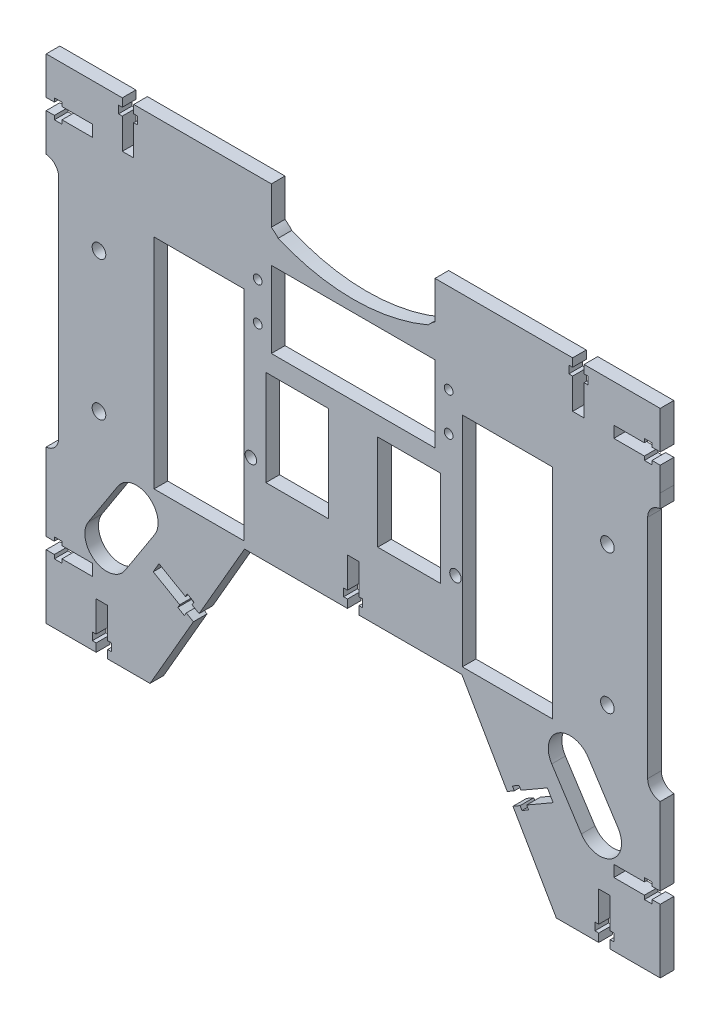
SolidWorks part; units mm, degrees
ref_plane "Front Plane" through (0, 0, 0) normal (0, 0, 1) x (1, 0, 0)
ref_plane "Top Plane" through (0, 0, 0) normal (0, 1, 0) x (1, 0, 0)
ref_plane "Right Plane" through (0, 0, 0) normal (1, 0, 0) x (0, 0, -1)
sketch "Sketch1" plane through (0, 0, 0) normal (0, 0, 1) x (1, 0, 0)
  line L40 (-72.729, 26.6154) -> (-39.729, 26.6154)
  line L41 (-72.729, 26.6154) -> (-72.729, -53.3846)
  line L42 (-72.729, -53.3846) -> (-39.729, -53.3846)
  line L43 (-39.729, 26.6154) -> (-39.729, -53.3846)
  line L44 (-72.729, 26.6154) -> (-39.729, -53.3846) construction
  line L45 (-72.729, -53.3846) -> (-39.729, 26.6154) construction
  line L46 (-35.729, 4.1154) -> (-4.729, 4.1154)
  line L47 (-35.729, 4.1154) -> (-35.729, -30.8846)
  line L48 (-35.729, -30.8846) -> (-4.729, -30.8846)
  line L49 (-4.729, 4.1154) -> (-4.729, -30.8846)
  line L50 (-35.729, 4.1154) -> (-4.729, -30.8846) construction
  line L51 (-35.729, -30.8846) -> (-4.729, 4.1154) construction
  line L52 (5.271, 4.1154) -> (36.271, 4.1154)
  line L53 (5.271, 4.1154) -> (5.271, -30.8846)
  line L54 (5.271, -30.8846) -> (36.271, -30.8846)
  line L55 (36.271, 4.1154) -> (36.271, -30.8846)
  line L56 (5.271, 4.1154) -> (36.271, -30.8846) construction
  line L57 (5.271, -30.8846) -> (36.271, 4.1154) construction
  line L58 (71.8624, -120.8846) -> (117.841, -120.8846)
  line L59 (117.841, -120.8846) -> (117.841, -59.8774)
  line L60 (117.841, -59.8774) -> (113.241, -59.8774)
  line L61 (108.241, -54.8774) -> (108.241, 28.1082)
  line L62 (113.241, 33.1082) -> (117.8396, 33.1082)
  line L63 (117.8396, 33.1082) -> (117.8393, 49.9036)
  line L64 (117.8393, 49.9036) -> (117.8223, 69.9688)
  line L65 (117.8223, 69.9688) -> (36.9219, 69.9688)
  line L66 (-36.3799, 69.9688) -> (-117.2803, 69.9688)
  line L67 (-117.2803, 69.9688) -> (-117.2973, 49.9036)
  line L68 (-117.2973, 49.9036) -> (-117.2977, 33.1082)
  line L69 (-117.2977, 33.1082) -> (-112.699, 33.1082)
  line L70 (-107.699, 28.1082) -> (-107.699, -54.8774)
  line L71 (-112.699, -59.8774) -> (-117.299, -59.8774)
  line L72 (-117.299, -59.8774) -> (-117.299, -120.8846)
  line L73 (-117.299, -120.8846) -> (-71.3205, -120.8846)
  line L74 (-71.3205, -120.8846) -> (-36.6794, -60.8846)
  line L75 (-36.6794, -60.8846) -> (37.2214, -60.8846)
  line L76 (37.2214, -60.8846) -> (71.8624, -120.8846)
  line L77 (71.8624, -120.8846) -> (117.841, -120.8846)
  line L78 (117.841, -120.8846) -> (117.841, -59.8774)
  line L79 (117.841, -59.8774) -> (113.241, -59.8774)
  line L80 (108.241, -54.8774) -> (108.241, 28.1082)
  line L81 (113.241, 33.1082) -> (117.8396, 33.1082)
  line L82 (117.8396, 33.1082) -> (117.8393, 49.9036)
  line L83 (117.8393, 49.9036) -> (117.8223, 69.9688)
  line L84 (117.8223, 69.9688) -> (36.9219, 69.9688)
  line L85 (-36.3799, 69.9688) -> (-117.2803, 69.9688)
  line L86 (-117.2803, 69.9688) -> (-117.2973, 49.9036)
  line L87 (-117.2973, 49.9036) -> (-117.2977, 33.1082)
  line L88 (-117.2977, 33.1082) -> (-112.699, 33.1082)
  line L89 (-107.699, 28.1082) -> (-107.699, -54.8774)
  line L90 (-112.699, -59.8774) -> (-117.299, -59.8774)
  line L91 (-117.299, -59.8774) -> (-117.299, -120.8846)
  line L92 (-117.299, -120.8846) -> (-71.3205, -120.8846)
  line L93 (-71.3205, -120.8846) -> (-36.6794, -60.8846)
  line L94 (-36.6794, -60.8846) -> (37.2214, -60.8846)
  line L95 (37.2214, -60.8846) -> (71.8624, -120.8846)
  line L96 (40.271, 26.6154) -> (73.271, 26.6154)
  line L97 (40.271, 26.6154) -> (40.271, -53.3846)
  line L98 (40.271, -53.3846) -> (73.271, -53.3846)
  line L99 (73.271, 26.6154) -> (73.271, -53.3846)
  line L100 (40.271, 26.6154) -> (73.271, -53.3846) construction
  line L101 (40.271, -53.3846) -> (73.271, 26.6154) construction
  circle A37 centre (-92.929, 12.1154) radius 2.5
  circle A38 centre (-92.929, -38.8846) radius 2.5
  circle A39 centre (93.471, 12.1154) radius 2.5
  circle A40 centre (93.471, -38.8846) radius 2.5
  arc A42 (108.241, -54.8774) -> (113.241, -59.8774) centre (113.241, -54.8774) ccw
  arc A43 (113.241, 33.1082) -> (108.241, 28.1082) centre (113.241, 28.1082) ccw
  arc A44 (-36.3799, 69.9688) -> (36.9219, 69.9688) centre (0.271, 135.4036) ccw
  arc A45 (-107.699, 28.1082) -> (-112.699, 33.1082) centre (-112.699, 28.1082) ccw
  arc A46 (-112.699, -59.8774) -> (-107.699, -54.8774) centre (-112.699, -54.8774) ccw
  arc A47 (108.241, -54.8774) -> (113.241, -59.8774) centre (113.241, -54.8774) ccw
  arc A48 (113.241, 33.1082) -> (108.241, 28.1082) centre (113.241, 28.1082) ccw
  arc A49 (-36.3799, 69.9688) -> (36.9219, 69.9688) centre (0.271, 135.4036) ccw
  arc A50 (-107.699, 28.1082) -> (-112.699, 33.1082) centre (-112.699, 28.1082) ccw
  arc A51 (-112.699, -59.8774) -> (-107.699, -54.8774) centre (-112.699, -54.8774) ccw
  point P18 (-56.229, -13.3846)
  point P27 (-20.229, -13.3846)
  point P36 (20.771, -13.3846)
  point P45 (56.771, -13.3846)
  dimension "D1" = 0
extrude "Boss-Extrude1" add sketch "Sketch1" along normal blind 5
sketch "Sketch2" plane through (0, 0, 5) normal (0, 0, 1) x (1, 0, 0)
  line L0 (-29.729, 60.4036) -> (-29.729, 66.665)
  line L2 (-29.729, 60.4036) -> (-29.729, 32.4036)
  line L3 (-29.729, 32.4036) -> (30.271, 32.4036)
  line L4 (30.271, 60.4036) -> (30.271, 32.4036)
  line L5 (-29.729, 60.4036) -> (30.271, 32.4036) construction
  line L6 (-29.729, 32.4036) -> (30.271, 60.4036) construction
  line L7 (30.271, 60.4036) -> (30.271, 66.665)
  arc A0 (-36.3799, 69.9688) -> (36.9219, 69.9688) centre (0.271, 135.4036) ccw construction
  arc A1 (-29.729, 66.665) -> (30.271, 66.665) centre (0.271, 135.4036) ccw
  point P4 (0.271, 46.4036)
extrude "Cut-Extrude1" cut sketch "Sketch2" against normal blind 10
sketch "Sketch3" plane through (0, 0, 5) normal (0, 0, 1) x (1, 0, 0)
  circle A4 centre (35.271, 32.1154) radius 1.6
  circle A5 centre (35.271, 18.1154) radius 1.6
  circle A6 centre (-34.729, 32.1154) radius 1.6
  circle A7 centre (-34.729, 18.1154) radius 1.6
extrude "Cut-Extrude2" cut sketch "Sketch3" against normal blind 10
sketch "Sketch4" plane through (0, 0, 5) normal (0, 0, 1) x (1, 0, 0)
  line L3 (-112.299, -64.8694) -> (-112.299, -115.8846)
  line L4 (-112.299, -115.8846) -> (-74.2072, -115.8846)
  line L5 (-74.2072, -115.8846) -> (-39.5662, -55.8846)
  line L6 (-39.5662, -55.8846) -> (40.1081, -55.8846)
  line L7 (40.1081, -55.8846) -> (74.7492, -115.8846)
  line L9 (74.7492, -115.8846) -> (112.841, -115.8846)
  line L11 (112.841, -115.8846) -> (112.841, -64.8694)
  line L12 (112.841, -64.8694) -> (112.841, -64.8694)
  line L15 (112.8395, 38.1001) -> (112.8395, 38.1001)
  line L22 (112.8395, 38.1001) -> (112.8393, 49.9014)
  line L23 (112.8393, 49.9014) -> (112.8265, 64.9688)
  line L24 (112.8265, 64.9688) -> (38.2044, 64.9688)
  line L28 (-37.6624, 64.9688) -> (-112.2846, 64.9688)
  line L29 (-112.2846, 64.9688) -> (-112.2973, 49.9014)
  line L30 (-112.2973, 49.9014) -> (-112.2976, 38.1001)
  line L31 (-112.2976, 38.1001) -> (-112.2976, 38.1001)
  line L33 (-112.299, -64.8694) -> (-112.299, -64.8694)
  line L34 (-29.729, 32.4036) -> (-29.729, 66.665)
  line L35 (-36.3799, 69.9688) -> (-117.2803, 69.9688)
  line L36 (-117.2803, 69.9688) -> (-117.2973, 49.9036)
  line L37 (-117.2973, 49.9036) -> (-117.2977, 33.1082)
  line L38 (-117.2977, 33.1082) -> (-112.699, 33.1082)
  line L39 (-107.699, 28.1082) -> (-107.699, -54.8774)
  line L40 (-112.699, -59.8774) -> (-117.299, -59.8774)
  line L41 (-117.299, -59.8774) -> (-117.299, -120.8846)
  line L42 (-117.299, -120.8846) -> (-71.3205, -120.8846)
  line L43 (-71.3205, -120.8846) -> (-36.6794, -60.8846)
  line L66 (-36.6794, -60.8846) -> (37.2214, -60.8846)
  line L67 (37.2214, -60.8846) -> (71.8624, -120.8846)
  line L68 (71.8624, -120.8846) -> (117.841, -120.8846)
  line L69 (117.841, -120.8846) -> (117.841, -59.8774)
  line L70 (117.841, -59.8774) -> (113.241, -59.8774)
  line L71 (108.241, -54.8774) -> (108.241, 28.1082)
  line L72 (113.241, 33.1082) -> (117.8396, 33.1082)
  line L73 (117.8396, 33.1082) -> (117.8393, 49.9036)
  line L74 (117.8393, 49.9036) -> (117.8223, 69.9688)
  line L75 (117.8223, 69.9688) -> (36.9219, 69.9688)
  line L76 (30.271, 66.665) -> (30.271, 32.4036)
  line L77 (30.271, 32.4036) -> (-29.729, 32.4036)
  line L79 (-36.3799, 69.9688) -> (-117.2803, 69.9688)
  line L80 (-117.2803, 69.9688) -> (-117.2973, 49.9036)
  line L81 (-117.2973, 49.9036) -> (-117.2977, 33.1082)
  line L82 (-117.2977, 33.1082) -> (-112.699, 33.1082)
  line L84 (-112.699, -59.8774) -> (-117.299, -59.8774)
  line L85 (-117.299, -59.8774) -> (-117.299, -120.8846)
  line L86 (-117.299, -120.8846) -> (-71.3205, -120.8846)
  line L87 (-71.3205, -120.8846) -> (-36.6794, -60.8846)
  line L88 (-36.6794, -60.8846) -> (37.2214, -60.8846)
  line L89 (37.2214, -60.8846) -> (71.8624, -120.8846)
  line L90 (71.8624, -120.8846) -> (117.841, -120.8846)
  line L91 (117.841, -120.8846) -> (117.841, -59.8774)
  line L92 (117.841, -59.8774) -> (113.241, -59.8774)
  line L94 (113.241, 33.1082) -> (117.8396, 33.1082)
  line L95 (117.8396, 33.1082) -> (117.8393, 49.9036)
  line L96 (117.8393, 49.9036) -> (117.8223, 69.9688)
  line L97 (117.8223, 69.9688) -> (36.9219, 69.9688)
  line L100 (-112.299, -64.8694) -> (-112.299, -59.8614)
  line L101 (-112.2976, 38.1001) -> (-112.2976, 33.0921)
  line L102 (-107.699, 28.1082) -> (-107.699, -54.8774) construction
  line L103 (-102.699, 28.1082) -> (-102.699, -54.8774) construction
  line L104 (-36.3799, 69.9688) -> (-36.3799, 64.2931)
  line L105 (36.9219, 69.9688) -> (36.9219, 64.2931)
  line L106 (-29.729, 32.4036) -> (-29.729, 66.665) construction
  line L107 (-34.729, 27.4036) -> (-34.729, 63.4661) construction
  line L108 (30.271, 32.4036) -> (-29.729, 32.4036) construction
  line L109 (35.271, 27.4036) -> (-34.729, 27.4036) construction
  line L110 (112.8395, 38.1001) -> (112.8395, 33.0921)
  line L111 (30.271, 66.665) -> (30.271, 32.4036) construction
  line L112 (35.271, 63.4661) -> (35.271, 27.4036) construction
  line L113 (112.841, -64.8694) -> (112.841, -59.8614)
  line L114 (108.241, -54.8774) -> (108.241, 28.1082) construction
  line L115 (103.241, -54.8774) -> (103.241, 28.1082) construction
  arc A2 (36.9219, 64.2931) -> (38.2044, 64.9688) centre (0.271, 135.4036) ccw
  arc A3 (-37.6624, 64.9688) -> (-36.3799, 64.2931) centre (0.271, 135.4036) ccw
  arc A6 (-36.3799, 69.9688) -> (-29.729, 66.665) centre (0.271, 135.4036) ccw
  arc A7 (-107.699, 28.1082) -> (-112.699, 33.1082) centre (-112.699, 28.1082) ccw
  arc A8 (-112.699, -59.8774) -> (-107.699, -54.8774) centre (-112.699, -54.8774) ccw
  arc A9 (108.241, -54.8774) -> (113.241, -59.8774) centre (113.241, -54.8774) ccw
  arc A10 (113.241, 33.1082) -> (108.241, 28.1082) centre (113.241, 28.1082) ccw
  arc A11 (30.271, 66.665) -> (36.9219, 69.9688) centre (0.271, 135.4036) ccw
  arc A13 (-112.2976, 33.0921) -> (-112.699, 33.1082) centre (-112.699, 28.1082) ccw
  arc A14 (-112.699, -59.8774) -> (-112.299, -59.8614) centre (-112.699, -54.8774) ccw
  arc A15 (112.841, -59.8614) -> (113.241, -59.8774) centre (113.241, -54.8774) ccw
  arc A16 (113.241, 33.1082) -> (112.8395, 33.0921) centre (113.241, 28.1082) ccw
  arc A18 (-112.299, -64.8694) -> (-102.699, -54.8774) centre (-112.699, -54.8774) ccw construction
  arc A19 (-112.699, -59.8774) -> (-107.699, -54.8774) centre (-112.699, -54.8774) ccw construction
  arc A20 (-102.699, 28.1082) -> (-112.2976, 38.1001) centre (-112.699, 28.1082) ccw construction
  arc A21 (-107.699, 28.1082) -> (-112.699, 33.1082) centre (-112.699, 28.1082) ccw construction
  arc A22 (-37.6624, 64.9688) -> (-34.729, 63.4661) centre (0.271, 135.4036) ccw construction
  arc A23 (-36.3799, 69.9688) -> (-29.729, 66.665) centre (0.271, 135.4036) ccw construction
  arc A24 (35.271, 63.4661) -> (38.2044, 64.9688) centre (0.271, 135.4036) ccw construction
  arc A25 (30.271, 66.665) -> (36.9219, 69.9688) centre (0.271, 135.4036) ccw construction
  arc A26 (113.241, 33.1082) -> (108.241, 28.1082) centre (113.241, 28.1082) ccw construction
  arc A27 (112.8395, 38.1001) -> (103.241, 28.1082) centre (113.241, 28.1082) ccw construction
  arc A28 (103.241, -54.8774) -> (112.841, -64.8694) centre (113.241, -54.8774) ccw construction
  arc A29 (108.241, -54.8774) -> (113.241, -59.8774) centre (113.241, -54.8774) ccw construction
  dimension "D1" = 0
  dimension "D2" = 5
extrude "Cut-Extrude3" cut sketch "Sketch4" against normal blind 5 contours A15 L113 L11 L9 L7 L6 L5 L4 L3 L100 A14 L84 L85 L86 L87 L88 L89 L90 L91 L92 | A13 L101 L30 L29 L28 A3 L104 L79 L80 L81 L82 | A16 L94 L95 L96 L97 L105 A2 L24 L23 L22 L110
sketch "Sketch5" plane through (0, 0, 5) normal (0, 0, 1) x (1, 0, 0)
  line L0 (-36.3799, 64.9688) -> (-29.729, 64.9688)
  line L1 (-29.729, 66.665) -> (-29.729, 32.4036) construction
  line L2 (-36.3799, 69.9688) -> (-36.3799, 64.2931) construction
  line L3 (-29.729, 66.665) -> (-29.729, 64.9688)
  line L4 (-36.3799, 69.9688) -> (-36.3799, 64.9688)
  line L5 (0.271, -55.8846) -> (0.271, 93.8511) construction
  line L6 (-39.5662, -55.8846) -> (40.1081, -55.8846) construction
  line L7 (36.9219, 69.9688) -> (36.9219, 64.9688)
  line L8 (30.271, 66.665) -> (30.271, 64.9688)
  line L9 (36.9219, 64.9688) -> (30.271, 64.9688)
  arc A0 (-36.3799, 69.9688) -> (-29.729, 66.665) centre (0.271, 135.4036) ccw construction
  arc A1 (-36.3799, 69.9688) -> (-29.729, 66.665) centre (0.271, 135.4036) ccw
  arc A2 (36.9219, 69.9688) -> (30.271, 66.665) centre (0.271, 135.4036) cw
extrude "Cut-Extrude4" cut sketch "Sketch5" against normal blind 5
sketch "Sketch6" plane through (0, 0, 5) normal (0, 0, 1) x (1, 0, 0)
  line L7 (-37.6624, 64.9688) -> (-34.494, 64.9688)
  line L8 (-37.6624, 64.9688) -> (-37.6624, 62.0905)
  line L9 (-37.6624, 62.0905) -> (-34.494, 62.0905)
  line L10 (-34.494, 64.9688) -> (-34.494, 62.0905)
  line L11 (38.2044, 64.9688) -> (35.6866, 64.9688)
  line L12 (38.2044, 64.9688) -> (38.2044, 62.5595)
  line L13 (38.2044, 62.5595) -> (35.6866, 62.5595)
  line L14 (35.6866, 64.9688) -> (35.6866, 62.5595)
extrude "Boss-Extrude3" add sketch "Sketch6" against normal blind 5
sketch "Sketch7" plane through (0, 0, 5) normal (0, 0, 1) x (1, 0, 0)
  line L0 (-112.2799, 46.9388) -> (-112.3817, 46.9388) construction
  line L1 (95.8227, 51.1388) -> (95.8227, 46.9388) construction
  line L2 (107.0227, 51.1388) -> (95.8227, 51.1388) construction
  line L3 (107.0227, 52.5388) -> (107.0227, 51.1388) construction
  line L4 (109.8227, 52.5388) -> (107.0227, 52.5388) construction
  line L5 (109.8227, 51.1388) -> (109.8227, 52.5388) construction
  line L6 (112.8227, 51.1388) -> (109.8227, 51.1388) construction
  line L7 (112.8227, 51.136) -> (112.8227, 51.1388) construction
  line L8 (107.0227, 46.9388) -> (95.8227, 46.9388) construction
  line L9 (107.0227, 46.9388) -> (95.8227, 46.9388) construction
  line L10 (112.8227, 46.9388) -> (109.8227, 46.9388) construction
  line L11 (112.8227, 46.9388) -> (112.9244, 46.9388) construction
  line L12 (-1.8286, -55.8846) -> (2.3714, -55.8846)
  line L13 (-1.8286, -52.8846) -> (-1.8286, -55.8846)
  line L14 (-3.2286, -52.8846) -> (-1.8286, -52.8846)
  line L15 (-3.2286, -50.0846) -> (-3.2286, -52.8846)
  line L16 (-1.8286, -50.0846) -> (-3.2286, -50.0846)
  line L17 (-1.8286, -38.8846) -> (-1.8286, -50.0846)
  line L18 (2.3714, -38.8846) -> (-1.8286, -38.8846)
  line L19 (2.3714, -50.0846) -> (2.3714, -38.8846)
  line L20 (3.7714, -50.0846) -> (2.3714, -50.0846)
  line L21 (3.7714, -52.8846) -> (3.7714, -50.0846)
  line L22 (2.3714, -52.8846) -> (3.7714, -52.8846)
  line L23 (2.3714, -55.8846) -> (2.3714, -52.8846)
  line L24 (-1.8286, -55.8846) -> (2.3714, -55.8846)
  line L25 (-1.8286, -52.8846) -> (-1.8286, -55.8846)
  line L26 (-3.2286, -52.8846) -> (-1.8286, -52.8846)
  line L27 (-3.2286, -50.0846) -> (-3.2286, -52.8846)
  line L28 (-1.8286, -50.0846) -> (-3.2286, -50.0846)
  line L29 (-1.8286, -38.8846) -> (-1.8286, -50.0846)
  line L30 (2.3714, -38.8846) -> (-1.8286, -38.8846)
  line L31 (2.3714, -50.0846) -> (2.3714, -38.8846)
  line L32 (3.7714, -50.0846) -> (2.3714, -50.0846)
  line L33 (3.7714, -52.8846) -> (3.7714, -50.0846)
  line L34 (2.3714, -52.8846) -> (3.7714, -52.8846)
  line L35 (2.3714, -55.8846) -> (2.3714, -52.8846)
  line L36 (112.8227, 33.8158) -> (112.9244, 46.9388) construction
  line L37 (112.8227, 46.9388) -> (112.8227, 33.8158) construction
  line L38 (112.8227, 46.9388) -> (109.8227, 46.9388) construction
  line L39 (107.0227, 45.5388) -> (107.0227, 46.9388) construction
  line L40 (107.0227, 45.5388) -> (107.0227, 46.9388) construction
  line L41 (109.8227, 45.5388) -> (107.0227, 45.5388) construction
  line L42 (109.8227, 45.5388) -> (107.0227, 45.5388) construction
  line L43 (109.8227, 46.9388) -> (109.8227, 45.5388) construction
  line L44 (109.8227, 46.9388) -> (109.8227, 45.5388) construction
  line L45 (-112.2799, 49.0388) -> (-112.3308, 49.0388) construction
  line L46 (112.8227, 49.0388) -> (112.8736, 49.0388) construction
  line L47 (112.8219, 51.1388) -> (117.8396, 33.8334) construction
  line L48 (113.241, 33.8334) -> (117.8396, 33.8334) construction
  line L49 (-1.8286, -55.8846) -> (0.271, -55.8846) construction
  line L50 (-1.8286, -55.8846) -> (-1.8286, -52.8846) construction
  line L51 (-1.8286, -52.8846) -> (-3.2286, -52.8846) construction
  line L52 (-3.2286, -52.8846) -> (-3.2286, -50.0846) construction
  line L53 (-3.2286, -50.0846) -> (-1.8286, -50.0846) construction
  line L54 (-1.8286, -50.0846) -> (-1.8286, -38.8846) construction
  line L55 (-1.8286, -38.8846) -> (2.3714, -38.8846) construction
  line L56 (2.3714, -50.0846) -> (2.3714, -38.8846) construction
  line L57 (3.7714, -50.0846) -> (2.3714, -50.0846) construction
  line L58 (3.7714, -52.8846) -> (3.7714, -50.0846) construction
  line L59 (2.3714, -52.8846) -> (3.7714, -52.8846) construction
  line L60 (2.3714, -55.8846) -> (2.3714, -52.8846) construction
  line L61 (2.3714, -55.8846) -> (0.2718, -55.8846) construction
  line L62 (-56.2086, -84.7101) -> (-58.3086, -88.3474) construction
  line L63 (-58.3086, -88.3474) -> (-60.9066, -86.8474) construction
  line L64 (-60.9066, -86.8474) -> (-61.6066, -88.0598) construction
  line L65 (-61.6066, -88.0598) -> (-64.0315, -86.6598) construction
  line L66 (-64.0315, -86.6598) -> (-63.3315, -85.4474) construction
  line L67 (-63.3315, -85.4474) -> (-73.031, -79.8474) construction
  line L68 (-73.031, -79.8474) -> (-70.931, -76.2101) construction
  line L69 (-61.2315, -81.8101) -> (-70.931, -76.2101) construction
  line L70 (-60.5315, -80.5976) -> (-61.2315, -81.8101) construction
  line L71 (-58.1066, -81.9976) -> (-60.5315, -80.5976) construction
  line L72 (-58.8066, -83.2101) -> (-58.1066, -81.9976) construction
  line L73 (-56.2086, -84.7101) -> (-58.8066, -83.2101) construction
  line L74 (-112.299, -92.4796) -> (-112.299, -88.2796) construction
  line L75 (-112.299, -88.2796) -> (-109.299, -88.2796) construction
  line L76 (-109.299, -88.2796) -> (-109.299, -86.8796) construction
  line L77 (-109.299, -86.8796) -> (-106.499, -86.8796) construction
  line L78 (-106.499, -86.8796) -> (-106.499, -88.2796) construction
  line L79 (-106.499, -88.2796) -> (-95.299, -88.2796) construction
  line L80 (-95.299, -88.2796) -> (-95.299, -92.4796) construction
  line L81 (-106.499, -92.4796) -> (-95.299, -92.4796) construction
  line L82 (-106.499, -93.8796) -> (-106.499, -92.4796) construction
  line L83 (-109.299, -93.8796) -> (-106.499, -93.8796) construction
  line L84 (-109.299, -92.4796) -> (-109.299, -93.8796) construction
  line L85 (-112.299, -92.4796) -> (-109.299, -92.4796) construction
  line L86 (-89.754, -115.8846) -> (-93.954, -115.8846) construction
  line L87 (-93.954, -115.8846) -> (-93.954, -112.8846) construction
  line L88 (-93.954, -112.8846) -> (-95.354, -112.8846) construction
  line L89 (-95.354, -112.8846) -> (-95.354, -110.0846) construction
  line L90 (-95.354, -110.0846) -> (-93.954, -110.0846) construction
  line L91 (-93.954, -110.0846) -> (-93.954, -98.8846) construction
  line L92 (-93.954, -98.8846) -> (-89.754, -98.8846) construction
  line L93 (-89.754, -110.0846) -> (-89.754, -98.8846) construction
  line L94 (-88.354, -110.0846) -> (-89.754, -110.0846) construction
  line L95 (-88.354, -112.8846) -> (-88.354, -110.0846) construction
  line L96 (-89.754, -112.8846) -> (-88.354, -112.8846) construction
  line L97 (-89.754, -115.8846) -> (-89.754, -112.8846) construction
  line L98 (-112.2799, 46.9388) -> (-112.2799, 33.8158) construction
  line L99 (-112.699, 33.8334) -> (-112.2799, 51.1388) construction
  line L100 (-112.2799, 51.1388) -> (-109.2799, 51.1388) construction
  line L101 (-109.2799, 51.1388) -> (-109.2799, 52.5388) construction
  line L102 (-109.2799, 52.5388) -> (-106.4799, 52.5388) construction
  line L103 (-106.4799, 52.5388) -> (-106.4799, 51.1388) construction
  line L104 (-106.4799, 51.1388) -> (-95.2799, 51.1388) construction
  line L105 (-95.2799, 51.1388) -> (-95.2799, 46.9388) construction
  line L106 (-106.4799, 46.9388) -> (-95.2799, 46.9388) construction
  line L107 (-106.4799, 45.5388) -> (-106.4799, 46.9388) construction
  line L108 (-109.2799, 45.5388) -> (-106.4799, 45.5388) construction
  line L109 (-109.2799, 46.9388) -> (-109.2799, 45.5388) construction
  line L110 (-112.2799, 46.9388) -> (-109.2799, 46.9388) construction
  line L111 (-78.9299, 47.9688) -> (-74.7299, 47.9688) construction
  line L112 (-74.7299, 59.1688) -> (-74.7299, 47.9688) construction
  line L113 (-73.3299, 59.1688) -> (-74.7299, 59.1688) construction
  line L114 (-73.3299, 61.9688) -> (-73.3299, 59.1688) construction
  line L115 (-74.7299, 61.9688) -> (-73.3299, 61.9688) construction
  line L116 (-74.7299, 64.9688) -> (-74.7299, 61.9688) construction
  line L117 (-76.8299, 64.9688) -> (-74.7299, 64.9688) construction
  line L118 (-76.8299, 64.9688) -> (-78.9299, 64.9688) construction
  line L119 (-78.9299, 64.9688) -> (-78.9299, 61.9688) construction
  line L120 (-78.9299, 61.9688) -> (-80.3299, 61.9688) construction
  line L121 (-80.3299, 61.9688) -> (-80.3299, 59.1688) construction
  line L122 (-80.3299, 59.1688) -> (-78.9299, 59.1688) construction
  line L123 (-78.9299, 59.1688) -> (-78.9299, 47.9688) construction
  line L124 (63.8743, -85.4474) -> (73.5738, -79.8474) construction
  line L125 (64.5743, -86.6598) -> (63.8743, -85.4474) construction
  line L126 (62.1494, -88.0598) -> (64.5743, -86.6598) construction
  line L127 (61.4494, -86.8474) -> (62.1494, -88.0598) construction
  line L128 (58.8514, -88.3474) -> (61.4494, -86.8474) construction
  line L129 (56.7514, -84.7101) -> (58.8514, -88.3474) construction
  line L130 (56.7514, -84.7101) -> (59.3494, -83.2101) construction
  line L131 (59.3494, -83.2101) -> (58.6494, -81.9976) construction
  line L132 (58.6494, -81.9976) -> (61.0743, -80.5976) construction
  line L133 (61.0743, -80.5976) -> (61.7743, -81.8101) construction
  line L134 (61.7743, -81.8101) -> (71.4738, -76.2101) construction
  line L135 (73.5738, -79.8474) -> (71.4738, -76.2101) construction
  line L136 (79.4727, 61.9688) -> (80.8727, 61.9688) construction
  line L137 (79.4727, 64.9688) -> (79.4727, 61.9688) construction
  line L138 (77.3727, 64.9688) -> (79.4727, 64.9688) construction
  line L139 (77.3727, 64.9688) -> (75.2727, 64.9688) construction
  line L140 (75.2727, 64.9688) -> (75.2727, 61.9688) construction
  line L141 (75.2727, 61.9688) -> (73.8727, 61.9688) construction
  line L142 (73.8727, 61.9688) -> (73.8727, 59.1688) construction
  line L143 (73.8727, 59.1688) -> (75.2727, 59.1688) construction
  line L144 (75.2727, 59.1688) -> (75.2727, 47.9688) construction
  line L145 (79.4727, 47.9688) -> (75.2727, 47.9688) construction
  line L146 (79.4727, 59.1688) -> (79.4727, 47.9688) construction
  line L147 (80.8727, 59.1688) -> (79.4727, 59.1688) construction
  line L148 (80.8727, 61.9688) -> (80.8727, 59.1688) construction
  line L149 (94.4968, -110.0846) -> (94.4968, -98.8846) construction
  line L150 (95.8968, -110.0846) -> (94.4968, -110.0846) construction
  line L151 (95.8968, -112.8846) -> (95.8968, -110.0846) construction
  line L152 (94.4968, -112.8846) -> (95.8968, -112.8846) construction
  line L153 (94.4968, -115.8846) -> (94.4968, -112.8846) construction
  line L154 (90.2968, -115.8846) -> (94.4968, -115.8846) construction
  line L155 (90.2968, -115.8846) -> (90.2968, -112.8846) construction
  line L156 (90.2968, -112.8846) -> (88.8968, -112.8846) construction
  line L157 (88.8968, -112.8846) -> (88.8968, -110.0846) construction
  line L158 (88.8968, -110.0846) -> (90.2968, -110.0846) construction
  line L159 (90.2968, -110.0846) -> (90.2968, -98.8846) construction
  line L160 (94.4968, -98.8846) -> (90.2968, -98.8846) construction
  line L161 (112.8418, -88.2796) -> (109.8418, -88.2796) construction
  line L162 (112.8418, -92.4796) -> (112.8418, -88.2796) construction
  line L163 (112.8418, -92.4796) -> (109.8418, -92.4796) construction
  line L164 (109.8418, -92.4796) -> (109.8418, -93.8796) construction
  line L165 (109.8418, -93.8796) -> (107.0418, -93.8796) construction
  line L166 (107.0418, -93.8796) -> (107.0418, -92.4796) construction
  line L167 (107.0418, -92.4796) -> (95.8418, -92.4796) construction
  line L168 (95.8418, -88.2796) -> (95.8418, -92.4796) construction
  line L169 (107.0418, -88.2796) -> (95.8418, -88.2796) construction
  line L170 (107.0418, -86.8796) -> (107.0418, -88.2796) construction
  line L171 (109.8418, -86.8796) -> (107.0418, -86.8796) construction
  line L172 (109.8418, -88.2796) -> (109.8418, -86.8796) construction
  line L173 (117.841, -59.1523) -> (112.841, -59.8746) construction
  line L174 (112.841, -59.8746) -> (112.841, -59.1362) construction
  line L175 (117.841, -59.1523) -> (113.241, -59.1523) construction
  line L176 (-112.2982, -59.8746) -> (-112.2982, -59.1362) construction
  line L177 (-117.2982, -59.1523) -> (-112.6982, -59.1523) construction
  line L178 (-117.2982, -59.1523) -> (-112.2982, -59.8746) construction
  line L179 (-112.2799, 46.9388) -> (-112.3817, 46.9388)
  line L180 (95.8227, 51.1388) -> (95.8227, 46.9388)
  line L181 (107.0227, 51.1388) -> (95.8227, 51.1388)
  line L182 (107.0227, 52.5388) -> (107.0227, 51.1388)
  line L183 (109.8227, 52.5388) -> (107.0227, 52.5388)
  line L184 (109.8227, 51.1388) -> (109.8227, 52.5388)
  line L185 (112.8227, 51.1388) -> (109.8227, 51.1388)
  line L186 (112.8227, 51.136) -> (112.8227, 51.1388)
  line L187 (107.0227, 46.9388) -> (95.8227, 46.9388)
  line L188 (107.0227, 46.9388) -> (95.8227, 46.9388)
  line L189 (112.8227, 46.9388) -> (109.8227, 46.9388)
  line L190 (112.8227, 46.9388) -> (112.9244, 46.9388)
  line L191 (112.8227, 33.8158) -> (112.9244, 46.9388)
  line L192 (112.8227, 46.9388) -> (112.8227, 33.8158)
  line L193 (112.8227, 46.9388) -> (109.8227, 46.9388)
  line L194 (107.0227, 45.5388) -> (107.0227, 46.9388)
  line L195 (107.0227, 45.5388) -> (107.0227, 46.9388)
  line L196 (109.8227, 45.5388) -> (107.0227, 45.5388)
  line L197 (109.8227, 45.5388) -> (107.0227, 45.5388)
  line L198 (109.8227, 46.9388) -> (109.8227, 45.5388)
  line L199 (109.8227, 46.9388) -> (109.8227, 45.5388)
  line L200 (-112.2799, 49.0388) -> (-112.3308, 49.0388)
  line L201 (112.8227, 49.0388) -> (112.8736, 49.0388)
  line L202 (112.8219, 51.1388) -> (117.8396, 33.8334)
  line L203 (113.241, 33.8334) -> (117.8396, 33.8334)
  line L204 (-1.8286, -55.8846) -> (0.271, -55.8846)
  line L205 (-1.8286, -55.8846) -> (-1.8286, -52.8846)
  line L206 (-1.8286, -52.8846) -> (-3.2286, -52.8846)
  line L207 (-3.2286, -52.8846) -> (-3.2286, -50.0846)
  line L208 (-3.2286, -50.0846) -> (-1.8286, -50.0846)
  line L209 (-1.8286, -50.0846) -> (-1.8286, -38.8846)
  line L210 (-1.8286, -38.8846) -> (2.3714, -38.8846)
  line L211 (2.3714, -50.0846) -> (2.3714, -38.8846)
  line L212 (3.7714, -50.0846) -> (2.3714, -50.0846)
  line L213 (3.7714, -52.8846) -> (3.7714, -50.0846)
  line L214 (2.3714, -52.8846) -> (3.7714, -52.8846)
  line L215 (2.3714, -55.8846) -> (2.3714, -52.8846)
  line L216 (2.3714, -55.8846) -> (0.2718, -55.8846)
  line L217 (-56.2086, -84.7101) -> (-58.3086, -88.3474)
  line L218 (-58.3086, -88.3474) -> (-60.9066, -86.8474)
  line L219 (-60.9066, -86.8474) -> (-61.6066, -88.0598)
  line L220 (-61.6066, -88.0598) -> (-64.0315, -86.6598)
  line L221 (-64.0315, -86.6598) -> (-63.3315, -85.4474)
  line L222 (-63.3315, -85.4474) -> (-73.031, -79.8474)
  line L223 (-73.031, -79.8474) -> (-70.931, -76.2101)
  line L224 (-61.2315, -81.8101) -> (-70.931, -76.2101)
  line L225 (-60.5315, -80.5976) -> (-61.2315, -81.8101)
  line L226 (-58.1066, -81.9976) -> (-60.5315, -80.5976)
  line L227 (-58.8066, -83.2101) -> (-58.1066, -81.9976)
  line L228 (-56.2086, -84.7101) -> (-58.8066, -83.2101)
  line L229 (-112.299, -92.4796) -> (-112.299, -88.2796)
  line L230 (-112.299, -88.2796) -> (-109.299, -88.2796)
  line L231 (-109.299, -88.2796) -> (-109.299, -86.8796)
  line L232 (-109.299, -86.8796) -> (-106.499, -86.8796)
  line L233 (-106.499, -86.8796) -> (-106.499, -88.2796)
  line L234 (-106.499, -88.2796) -> (-95.299, -88.2796)
  line L235 (-95.299, -88.2796) -> (-95.299, -92.4796)
  line L236 (-106.499, -92.4796) -> (-95.299, -92.4796)
  line L237 (-106.499, -93.8796) -> (-106.499, -92.4796)
  line L238 (-109.299, -93.8796) -> (-106.499, -93.8796)
  line L239 (-109.299, -92.4796) -> (-109.299, -93.8796)
  line L240 (-112.299, -92.4796) -> (-109.299, -92.4796)
  line L241 (-89.754, -115.8846) -> (-93.954, -115.8846)
  line L242 (-93.954, -115.8846) -> (-93.954, -112.8846)
  line L243 (-93.954, -112.8846) -> (-95.354, -112.8846)
  line L244 (-95.354, -112.8846) -> (-95.354, -110.0846)
  line L245 (-95.354, -110.0846) -> (-93.954, -110.0846)
  line L246 (-93.954, -110.0846) -> (-93.954, -98.8846)
  line L247 (-93.954, -98.8846) -> (-89.754, -98.8846)
  line L248 (-89.754, -110.0846) -> (-89.754, -98.8846)
  line L249 (-88.354, -110.0846) -> (-89.754, -110.0846)
  line L250 (-88.354, -112.8846) -> (-88.354, -110.0846)
  line L251 (-89.754, -112.8846) -> (-88.354, -112.8846)
  line L252 (-89.754, -115.8846) -> (-89.754, -112.8846)
  line L253 (-112.2799, 46.9388) -> (-112.2799, 33.8158)
  line L254 (-112.699, 33.8334) -> (-112.2799, 51.1388)
  line L255 (-112.2799, 51.1388) -> (-109.2799, 51.1388)
  line L256 (-109.2799, 51.1388) -> (-109.2799, 52.5388)
  line L257 (-109.2799, 52.5388) -> (-106.4799, 52.5388)
  line L258 (-106.4799, 52.5388) -> (-106.4799, 51.1388)
  line L259 (-106.4799, 51.1388) -> (-95.2799, 51.1388)
  line L260 (-95.2799, 51.1388) -> (-95.2799, 46.9388)
  line L261 (-106.4799, 46.9388) -> (-95.2799, 46.9388)
  line L262 (-106.4799, 45.5388) -> (-106.4799, 46.9388)
  line L263 (-109.2799, 45.5388) -> (-106.4799, 45.5388)
  line L264 (-109.2799, 46.9388) -> (-109.2799, 45.5388)
  line L265 (-112.2799, 46.9388) -> (-109.2799, 46.9388)
  line L266 (-78.9299, 47.9688) -> (-74.7299, 47.9688)
  line L267 (-74.7299, 59.1688) -> (-74.7299, 47.9688)
  line L268 (-73.3299, 59.1688) -> (-74.7299, 59.1688)
  line L269 (-73.3299, 61.9688) -> (-73.3299, 59.1688)
  line L270 (-74.7299, 61.9688) -> (-73.3299, 61.9688)
  line L271 (-74.7299, 64.9688) -> (-74.7299, 61.9688)
  line L272 (-76.8299, 64.9688) -> (-74.7299, 64.9688)
  line L273 (-76.8299, 64.9688) -> (-78.9299, 64.9688)
  line L274 (-78.9299, 64.9688) -> (-78.9299, 61.9688)
  line L275 (-78.9299, 61.9688) -> (-80.3299, 61.9688)
  line L276 (-80.3299, 61.9688) -> (-80.3299, 59.1688)
  line L277 (-80.3299, 59.1688) -> (-78.9299, 59.1688)
  line L278 (-78.9299, 59.1688) -> (-78.9299, 47.9688)
  line L279 (63.8743, -85.4474) -> (73.5738, -79.8474)
  line L280 (64.5743, -86.6598) -> (63.8743, -85.4474)
  line L281 (62.1494, -88.0598) -> (64.5743, -86.6598)
  line L282 (61.4494, -86.8474) -> (62.1494, -88.0598)
  line L283 (58.8514, -88.3474) -> (61.4494, -86.8474)
  line L284 (56.7514, -84.7101) -> (58.8514, -88.3474)
  line L285 (56.7514, -84.7101) -> (59.3494, -83.2101)
  line L286 (59.3494, -83.2101) -> (58.6494, -81.9976)
  line L287 (58.6494, -81.9976) -> (61.0743, -80.5976)
  line L288 (61.0743, -80.5976) -> (61.7743, -81.8101)
  line L289 (61.7743, -81.8101) -> (71.4738, -76.2101)
  line L290 (73.5738, -79.8474) -> (71.4738, -76.2101)
  line L291 (79.4727, 61.9688) -> (80.8727, 61.9688)
  line L292 (79.4727, 64.9688) -> (79.4727, 61.9688)
  line L293 (77.3727, 64.9688) -> (79.4727, 64.9688)
  line L294 (77.3727, 64.9688) -> (75.2727, 64.9688)
  line L295 (75.2727, 64.9688) -> (75.2727, 61.9688)
  line L296 (75.2727, 61.9688) -> (73.8727, 61.9688)
  line L297 (73.8727, 61.9688) -> (73.8727, 59.1688)
  line L298 (73.8727, 59.1688) -> (75.2727, 59.1688)
  line L299 (75.2727, 59.1688) -> (75.2727, 47.9688)
  line L300 (79.4727, 47.9688) -> (75.2727, 47.9688)
  line L301 (79.4727, 59.1688) -> (79.4727, 47.9688)
  line L302 (80.8727, 59.1688) -> (79.4727, 59.1688)
  line L303 (80.8727, 61.9688) -> (80.8727, 59.1688)
  line L304 (94.4968, -110.0846) -> (94.4968, -98.8846)
  line L305 (95.8968, -110.0846) -> (94.4968, -110.0846)
  line L306 (95.8968, -112.8846) -> (95.8968, -110.0846)
  line L307 (94.4968, -112.8846) -> (95.8968, -112.8846)
  line L308 (94.4968, -115.8846) -> (94.4968, -112.8846)
  line L309 (90.2968, -115.8846) -> (94.4968, -115.8846)
  line L310 (90.2968, -115.8846) -> (90.2968, -112.8846)
  line L311 (90.2968, -112.8846) -> (88.8968, -112.8846)
  line L312 (88.8968, -112.8846) -> (88.8968, -110.0846)
  line L313 (88.8968, -110.0846) -> (90.2968, -110.0846)
  line L314 (90.2968, -110.0846) -> (90.2968, -98.8846)
  line L315 (94.4968, -98.8846) -> (90.2968, -98.8846)
  line L316 (112.8418, -88.2796) -> (109.8418, -88.2796)
  line L317 (112.8418, -92.4796) -> (112.8418, -88.2796)
  line L318 (112.8418, -92.4796) -> (109.8418, -92.4796)
  line L319 (109.8418, -92.4796) -> (109.8418, -93.8796)
  line L320 (109.8418, -93.8796) -> (107.0418, -93.8796)
  line L321 (107.0418, -93.8796) -> (107.0418, -92.4796)
  line L322 (107.0418, -92.4796) -> (95.8418, -92.4796)
  line L323 (95.8418, -88.2796) -> (95.8418, -92.4796)
  line L324 (107.0418, -88.2796) -> (95.8418, -88.2796)
  line L325 (107.0418, -86.8796) -> (107.0418, -88.2796)
  line L326 (109.8418, -86.8796) -> (107.0418, -86.8796)
  line L327 (109.8418, -88.2796) -> (109.8418, -86.8796)
  line L328 (117.841, -59.1523) -> (112.841, -59.8746)
  line L329 (112.841, -59.8746) -> (112.841, -59.1362)
  line L330 (117.841, -59.1523) -> (113.241, -59.1523)
  line L331 (-112.2982, -59.8746) -> (-112.2982, -59.1362)
  line L332 (-117.2982, -59.1523) -> (-112.6982, -59.1523)
  line L333 (-117.2982, -59.1523) -> (-112.2982, -59.8746)
  arc A0 (113.2418, 33.8334) -> (112.8227, 33.8158) centre (113.2418, 28.8334) ccw construction
  arc A1 (-112.2799, 33.8158) -> (-112.699, 33.8334) centre (-112.699, 28.8334) ccw construction
  arc A2 (112.841, -59.1362) -> (113.241, -59.1523) centre (113.241, -54.1523) ccw construction
  arc A3 (-112.6982, -59.1523) -> (-112.2982, -59.1362) centre (-112.6982, -54.1523) ccw construction
  arc A4 (113.2418, 33.8334) -> (112.8227, 33.8158) centre (113.2418, 28.8334) ccw
  arc A5 (-112.2799, 33.8158) -> (-112.699, 33.8334) centre (-112.699, 28.8334) ccw
  arc A6 (112.841, -59.1362) -> (113.241, -59.1523) centre (113.241, -54.1523) ccw
  arc A7 (-112.6982, -59.1523) -> (-112.2982, -59.1362) centre (-112.6982, -54.1523) ccw
  dimension "D1" = 0
extrude "Cut-Extrude5" cut sketch "Sketch7" against normal blind 5
sketch "Sketch8" plane through (0, 0, 5) normal (0, 0, 1) x (1, 0, 0)
  line L0 (59.3494, -83.2101) -> (55.7221, -85.3043)
  line L1 (-109.2799, 51.1388) -> (-113.4655, 51.1388)
  line L2 (-109.2799, 51.1388) -> (-109.2799, 49.8113)
  line L3 (-109.2799, 49.8113) -> (-113.4655, 49.8113)
  line L4 (-113.4655, 51.1388) -> (-113.4655, 49.8113)
  line L5 (55.7221, -85.3043) -> (57.8221, -88.9416)
  line L6 (61.4494, -86.8474) -> (57.8221, -88.9416)
  line L7 (59.3494, -83.2101) -> (61.4494, -86.8474)
extrude "Cut-Extrude6" cut sketch "Sketch8" against normal blind 5
sketch "Sketch9" plane through (0, 0, 5) normal (0, 0, 1) x (1, 0, 0)
  line L0 (-29.729, 32.4036) -> (-29.729, 11.1154)
  line L1 (-29.729, 11.1154) -> (30.271, 11.1154)
  line L2 (30.271, 11.1154) -> (30.271, 32.4036)
  line L3 (30.271, 32.4036) -> (-29.729, 32.4036)
extrude "Cut-Extrude7" cut sketch "Sketch9" against normal blind 10
sketch "Sketch10" plane through (0, 0, 0) normal (0, 0, -1) x (-1, 0, 0)
  line L0 (-30.271, 11.1154) -> (-30.271, 64.9688) construction
  line L1 (-30.271, 39.1154) -> (29.729, 39.1154)
  line L2 (-30.271, 39.1154) -> (-30.271, 51.203)
  line L4 (29.729, 39.1154) -> (29.729, 51.203)
  line L5 (-30.271, 39.1154) -> (29.729, 51.203) construction
  line L6 (-0.271, 45.1592) -> (29.729, 39.1154) construction
  line L7 (39.729, 39.1154) -> (-40.271, 39.1154) construction
  line L8 (29.729, 64.9688) -> (29.729, 11.1154) construction
  arc A3 (29.729, 51.203) -> (27.229, 48.9511) centre (38.4549, 39.0023) ccw
  arc A4 (-27.771, 48.9511) -> (-30.271, 51.203) centre (-38.9969, 39.0023) ccw
  arc A5 (-27.771, 48.9511) -> (27.229, 48.9511) centre (-0.271, 113.323) ccw
  point P4 (-0.271, 45.1592)
extrude "Boss-Extrude4" add sketch "Sketch10" against normal blind 5
ref_plane "Plane1" through (-31.729, -35.8846, -7) normal (0, -1, 0) x (-1, 0, 0)
sketch "Sketch13" plane through (0, 0, 5) normal (0, 0, 1) x (1, 0, 0)
  line L0 (32.271, -35.8846) -> (32.271, 9.1154) construction
  line L1 (9.271, 9.1154) -> (9.271, -35.8846) construction
  line L2 (-8.729, -35.8846) -> (-8.729, 9.1154) construction
  line L3 (-31.729, 9.1154) -> (-31.729, -35.8846) construction
  line L4 (32.271, -30.8846) -> (32.271, 4.1154)
  line L5 (9.271, 4.1154) -> (9.271, -30.8846)
  line L6 (-8.729, -30.8846) -> (-8.729, 4.1154)
  line L7 (-31.729, 4.1154) -> (-31.729, -30.8846)
  line L9 (-35.729, 4.1154) -> (-31.729, 4.1154)
  line L10 (-35.729, 4.1154) -> (-35.729, -30.8846)
  line L11 (-35.729, -30.8846) -> (-31.729, -30.8846)
  line L12 (-31.729, 4.1154) -> (-31.729, -30.8846)
  line L13 (36.271, 4.1154) -> (32.271, 4.1154)
  line L14 (36.271, 4.1154) -> (36.271, -30.8846)
  line L15 (36.271, -30.8846) -> (32.271, -30.8846)
  line L16 (32.271, 4.1154) -> (32.271, -30.8846)
  line L17 (-4.729, 4.1154) -> (-8.729, 4.1154)
  line L18 (-4.729, 4.1154) -> (-4.729, -30.8846)
  line L19 (-4.729, -30.8846) -> (-8.729, -30.8846)
  line L20 (-8.729, 4.1154) -> (-8.729, -30.8846)
  line L21 (5.271, 4.1154) -> (9.271, 4.1154)
  line L22 (5.271, 4.1154) -> (5.271, -30.8846)
  line L23 (5.271, -30.8846) -> (9.271, -30.8846)
  line L24 (9.271, 4.1154) -> (9.271, -30.8846)
extrude "Boss-Extrude5" add sketch "Sketch13" against normal blind 5 contours L10 L11 L7 L9 | L19 L18 L17 L6 | L22 L23 L5 L21 | L15 L14 L13 L4
ref_plane "Plane2" through (35.271, -20.6687, 20) normal (0, -1, 0) x (-1, 0, 0)
sketch "Sketch15" plane through (0, 0, 5) normal (0, 0, 1) x (1, 0, 0)
  line L0 (35.271, -20.6687) -> (35.271, -30.6687) construction
  line L1 (35.271, -20.6687) -> (35.271, -30.6687) construction
  line L2 (35.271, -25.6687) -> (40.271, -25.6687) construction
  line L3 (40.271, 26.6154) -> (40.271, -53.3846) construction
  line L4 (0.271, 11.1154) -> (0.271, -19.583) construction
  line L5 (-29.729, 11.1154) -> (30.271, 11.1154) construction
  circle A0 centre (37.771, -25.6687) radius 2.1
  circle A1 centre (-37.229, -25.6687) radius 2.1
  dimension "D1" = 4.2
extrude "Cut-Extrude8" cut sketch "Sketch15" against normal blind 5
sketch "Sketch16" plane through (0, 0, 5) normal (0, 0, 1) x (1, 0, 0)
  line L0 (-78.9299, 64.9688) -> (-78.9299, 61.9688) construction
  line L1 (-74.7299, 64.9688) -> (-74.7299, 61.9688) construction
  line L2 (-74.7299, 61.9688) -> (-73.3299, 61.9688) construction
  line L3 (-73.3299, 61.9688) -> (-73.3299, 59.1688) construction
  line L4 (-73.3299, 59.1688) -> (-74.7299, 59.1688) construction
  line L5 (-78.9299, 61.9688) -> (-80.3299, 61.9688) construction
  line L6 (-80.3299, 61.9688) -> (-80.3299, 59.1688) construction
  line L7 (-80.3299, 59.1688) -> (-78.9299, 59.1688) construction
  line L8 (-78.9299, 59.1688) -> (-78.9299, 47.9688) construction
  line L9 (-78.9299, 47.9688) -> (-74.7299, 47.9688) construction
  line L10 (-74.7299, 59.1688) -> (-74.7299, 47.9688) construction
  line L11 (80.8727, 59.1688) -> (79.4727, 59.1688) construction
  line L12 (80.8727, 61.9688) -> (80.8727, 59.1688) construction
  line L13 (79.4727, 61.9688) -> (80.8727, 61.9688) construction
  line L14 (79.4727, 64.9688) -> (79.4727, 61.9688) construction
  line L15 (75.2727, 64.9688) -> (75.2727, 61.9688) construction
  line L16 (75.2727, 61.9688) -> (73.8727, 61.9688) construction
  line L17 (73.8727, 61.9688) -> (73.8727, 59.1688) construction
  line L18 (73.8727, 59.1688) -> (75.2727, 59.1688) construction
  line L19 (79.4727, 47.9688) -> (75.2727, 47.9688) construction
  line L20 (75.2727, 59.1688) -> (75.2727, 47.9688) construction
  line L21 (79.4727, 59.1688) -> (79.4727, 47.9688) construction
  line L22 (-78.9299, 64.9688) -> (-78.9299, 61.9688)
  line L23 (-74.7299, 64.9688) -> (-74.7299, 61.9688)
  line L24 (-74.7299, 61.9688) -> (-73.3299, 61.9688)
  line L25 (-73.3299, 61.9688) -> (-73.3299, 59.1688)
  line L26 (-73.3299, 59.1688) -> (-74.7299, 59.1688)
  line L27 (-78.9299, 61.9688) -> (-80.3299, 61.9688)
  line L28 (-80.3299, 61.9688) -> (-80.3299, 59.1688)
  line L29 (-80.3299, 59.1688) -> (-78.9299, 59.1688)
  line L30 (-78.9299, 59.1688) -> (-78.9299, 47.9688)
  line L31 (-78.9299, 47.9688) -> (-74.7299, 47.9688)
  line L32 (-74.7299, 59.1688) -> (-74.7299, 47.9688)
  line L33 (80.8727, 59.1688) -> (79.4727, 59.1688)
  line L34 (80.8727, 61.9688) -> (80.8727, 59.1688)
  line L35 (79.4727, 61.9688) -> (80.8727, 61.9688)
  line L36 (79.4727, 64.9688) -> (79.4727, 61.9688)
  line L37 (75.2727, 64.9688) -> (75.2727, 61.9688)
  line L38 (75.2727, 61.9688) -> (73.8727, 61.9688)
  line L39 (73.8727, 61.9688) -> (73.8727, 59.1688)
  line L40 (73.8727, 59.1688) -> (75.2727, 59.1688)
  line L41 (79.4727, 47.9688) -> (75.2727, 47.9688)
  line L42 (75.2727, 59.1688) -> (75.2727, 47.9688)
  line L43 (79.4727, 59.1688) -> (79.4727, 47.9688)
  line L44 (-74.7299, 64.9688) -> (-78.9299, 64.9688)
  line L45 (75.2727, 64.9688) -> (79.4727, 64.9688)
extrude "Boss-Extrude6" add sketch "Sketch16" against normal blind 5
sketch "Sketch17" plane through (0, 0, 5) normal (0, 0, 1) x (1, 0, 0)
  line L12 (84.9223, 64.9688) -> (80.7223, 64.9688)
  line L13 (84.9223, 61.9688) -> (84.9223, 64.9688)
  line L14 (86.3223, 61.9688) -> (84.9223, 61.9688)
  line L15 (86.3223, 59.1688) -> (86.3223, 61.9688)
  line L16 (84.9223, 59.1688) -> (86.3223, 59.1688)
  line L17 (84.9223, 47.9688) -> (84.9223, 59.1688)
  line L18 (80.7223, 47.9688) -> (84.9223, 47.9688)
  line L19 (80.7223, 59.1688) -> (80.7223, 47.9688)
  line L20 (79.3223, 59.1688) -> (80.7223, 59.1688)
  line L21 (79.3223, 61.9688) -> (79.3223, 59.1688)
  line L22 (80.7223, 61.9688) -> (79.3223, 61.9688)
  line L23 (80.7223, 64.9688) -> (80.7223, 61.9688)
  line L24 (84.9223, 64.9688) -> (80.7223, 64.9688)
  line L25 (84.9223, 61.9688) -> (84.9223, 64.9688)
  line L26 (86.3223, 61.9688) -> (84.9223, 61.9688)
  line L27 (86.3223, 59.1688) -> (86.3223, 61.9688)
  line L28 (84.9223, 59.1688) -> (86.3223, 59.1688)
  line L29 (84.9223, 47.9688) -> (84.9223, 59.1688)
  line L30 (80.7223, 47.9688) -> (84.9223, 47.9688)
  line L31 (80.7223, 59.1688) -> (80.7223, 47.9688)
  line L32 (79.3223, 59.1688) -> (80.7223, 59.1688)
  line L33 (79.3223, 61.9688) -> (79.3223, 59.1688)
  line L34 (80.7223, 61.9688) -> (79.3223, 61.9688)
  line L35 (80.7223, 64.9688) -> (80.7223, 61.9688)
  line L48 (0.2714, -38.8846) -> (0.2714, 115.8122) construction
  line L49 (2.3714, -38.8846) -> (-1.8286, -38.8846) construction
  line L50 (-80.1795, 64.9688) -> (-80.1795, 61.9688)
  line L51 (-80.1795, 61.9688) -> (-78.7795, 61.9688)
  line L52 (-78.7795, 61.9688) -> (-78.7795, 59.1688)
  line L53 (-78.7795, 59.1688) -> (-80.1795, 59.1688)
  line L54 (-80.1795, 59.1688) -> (-80.1795, 47.9688)
  line L55 (-80.1795, 47.9688) -> (-84.3795, 47.9688)
  line L56 (-84.3795, 47.9688) -> (-84.3795, 59.1688)
  line L57 (-84.3795, 59.1688) -> (-85.7795, 59.1688)
  line L58 (-85.7795, 59.1688) -> (-85.7795, 61.9688)
  line L59 (-85.7795, 61.9688) -> (-84.3795, 61.9688)
  line L60 (-84.3795, 61.9688) -> (-84.3795, 64.9688)
  line L61 (-84.3795, 64.9688) -> (-80.1795, 64.9688)
  dimension "D1" = 0
extrude "Cut-Extrude9" cut sketch "Sketch17" against normal blind 5
sketch "Sketch18" plane through (0, 0, 5) normal (0, 0, 1) x (1, 0, 0)
  line L0 (-72.729, -53.3846) -> (-95.299, -88.2796) construction
  line L1 (0.2714, -38.8846) -> (0.2714, -123.0773) construction
  line L2 (2.3714, -38.8846) -> (-1.8286, -38.8846) construction
  line L3 (-90.1081, -80.2541) -> (-79.2462, -63.4607) construction
  line L6 (-96.8255, -75.9093) -> (-85.9635, -59.1159)
  line L7 (-83.3908, -84.5988) -> (-72.5288, -67.8054)
  line L10 (73.2718, -53.3846) -> (95.8418, -88.2796) construction
  line L11 (90.6509, -80.2541) -> (79.789, -63.4607) construction
  line L12 (97.3683, -75.9093) -> (86.5063, -59.1159)
  line L13 (83.9335, -84.5988) -> (73.0716, -67.8054)
  arc A0 (-96.8255, -75.9093) -> (-83.3908, -84.5988) centre (-90.1081, -80.2541) ccw
  arc A1 (-72.5288, -67.8054) -> (-85.9635, -59.1159) centre (-79.2462, -63.4607) ccw
  arc A2 (97.3683, -75.9093) -> (83.9335, -84.5988) centre (90.6509, -80.2541) cw
  arc A3 (73.0716, -67.8054) -> (86.5063, -59.1159) centre (79.789, -63.4607) cw
  point P8 (-84.6771, -71.8574)
  point P17 (85.2199, -71.8574)
  dimension "D1" = 8
  dimension "D2" = 20
  dimension "D3" = 12
extrude "Cut-Extrude11" cut sketch "Sketch18" against normal blind 5
